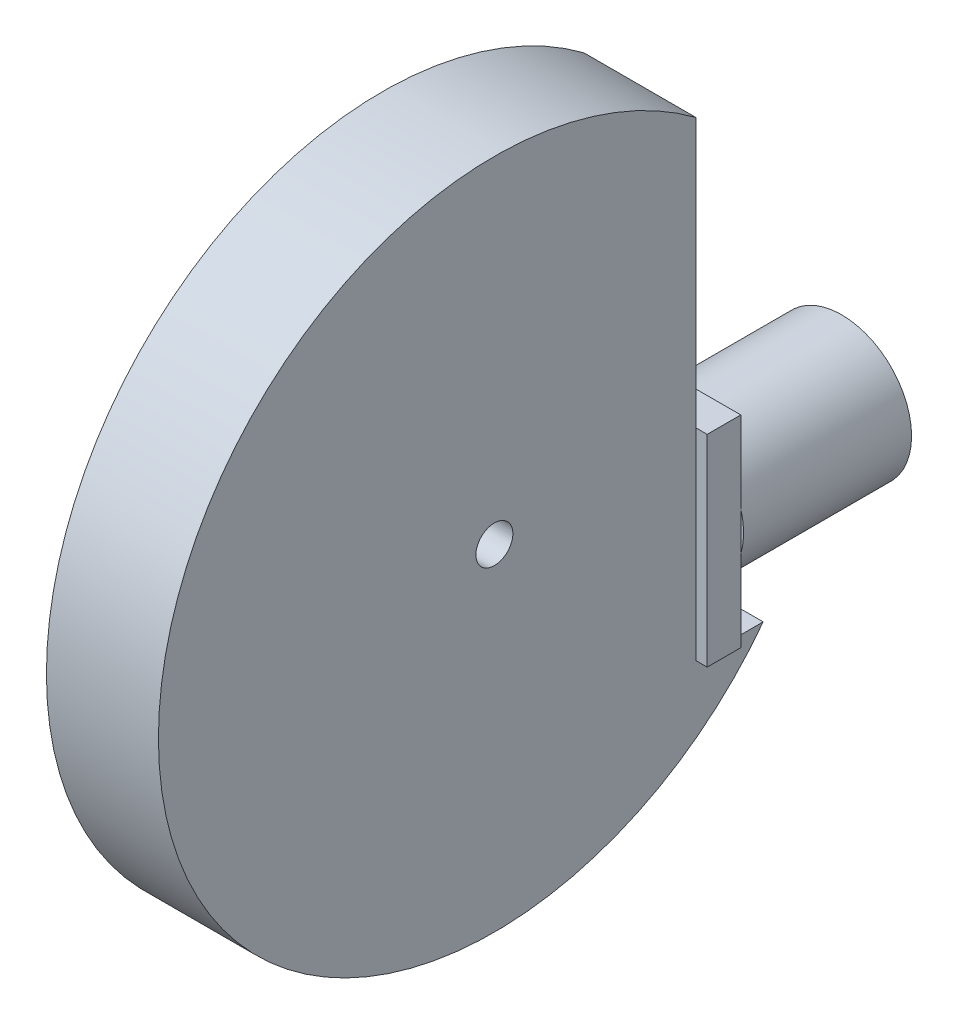
SolidWorks part; units mm, degrees
ref_plane "正面(Front)" through (0, 0, 0) normal (0, 0, 1) x (1, 0, 0)
ref_plane "平面(Top)" through (0, 0, 0) normal (0, 1, 0) x (1, 0, 0)
ref_plane "右側面(Right)" through (0, 0, 0) normal (1, 0, 0) x (0, 0, -1)
sketch "ｽｹｯﾁ2" plane through (0, 0, 0) normal (0, 0, 1) x (1, 0, 0)
  circle A0 centre (0, 0) radius 6.25
  dimension "D1" = 12.5
extrude "ﾎﾞｽ - 押し出し1" add sketch "ｽｹｯﾁ2" along normal blind 15
sketch "ｽｹｯﾁ3" plane through (0, 0, 15) normal (0, 0, 1) x (1, 0, 0)
  line L1 (-6, 9) -> (6, 9)
  line L2 (-6, 9) -> (-6, -9)
  line L3 (-6, -9) -> (6, -9)
  line L4 (6, 9) -> (6, -9)
  line L5 (-6, 9) -> (6, -9) construction
  line L6 (-6, -9) -> (6, 9) construction
  point P0 (0, 0)
  dimension "D1" = 18
  dimension "D2" = 12
extrude "ﾎﾞｽ - 押し出し2" add sketch "ｽｹｯﾁ3" along normal blind 3
sketch "ｽｹｯﾁ4" plane through (0, 0, 0) normal (1, 0, 0) x (0, 0, -1)
  line L3 (-18, 9) -> (-18, -9)
  line L4 (-18, 9) -> (-15, 9) construction
  line L5 (-18, -9) -> (-18, 9) construction
  line L6 (-18, 9) -> (-42.6287, 9) construction
  line L7 (-18, -9) -> (-15, -9) construction
  line L10 (-18, 33) -> (-18, 9)
  line L11 (-36, 9) -> (-36, 58.3167) construction
  line L12 (-12, -9) -> (-18, -9)
  arc A0 (-18, 33) -> (-12, -9) centre (-36, 9) ccw
  circle A1 centre (-36, 9) radius 1.65
  point P5 (-18, 33.0044)
  point P16 (-36, -21)
  point P17 (0, 0)
  point P18 (0, 0)
  point P19 (-11.9555, -9)
  point P20 (-12.5327, -9.6892)
  dimension "D2" = 30
  dimension "D4" = 18
  dimension "D1" = 18
  dimension "D3" = 3.3
extrude "ﾎﾞｽ - 押し出し3" add sketch "ｽｹｯﾁ4" along normal mid plane 10
